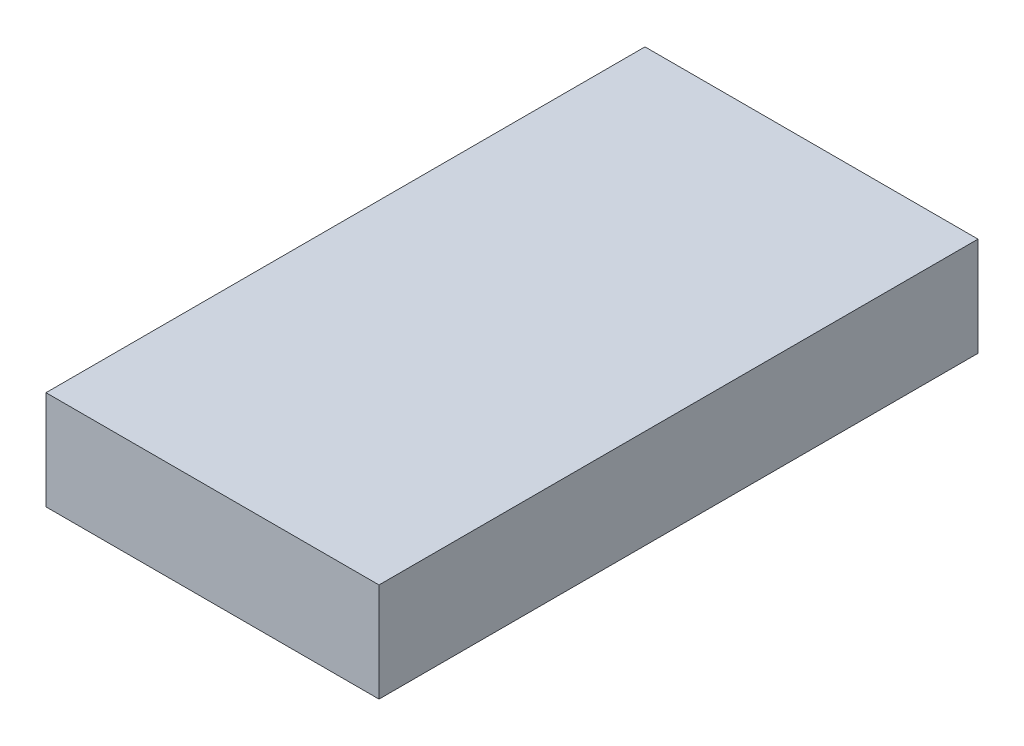
SolidWorks part; units mm, degrees
ref_plane "Front Plane" through (0, 0, 0) normal (0, 0, 1) x (1, 0, 0)
ref_plane "Top Plane" through (0, 0, 0) normal (0, 1, 0) x (1, 0, 0)
ref_plane "Right Plane" through (0, 0, 0) normal (1, 0, 0) x (0, 0, -1)
sketch "Sketch1" plane through (0, 0, 0) normal (0, 1, 0) x (1, 0, 0)
  line L1 (0, 0) -> (26, 0)
  line L2 (0, 0) -> (0, 46)
  line L3 (0, 46) -> (26, 46)
  line L4 (26, 0) -> (26, 46)
  dimension "D1" = 26
  dimension "D2" = 46
extrude "Boss-Extrude1" add sketch "Sketch1" along normal blind 5.8
sketch "Sketch2" plane through (0, 5.8, 0) normal (0, 1, 0) x (1, 0, 0)
  line L0 (0, 46) -> (0, 0) construction
  line L1 (0.65, 44.5) -> (25.35, 44.5)
  line L2 (0.65, 44.5) -> (0.65, -0.5)
  line L3 (0.65, -0.5) -> (25.35, -0.5)
  line L4 (25.35, 44.5) -> (25.35, -0.5)
  line L5 (26, 46) -> (0, 46) construction
  dimension "D1" = 24.7
  dimension "D2" = 45
  dimension "D3" = 0.65
  dimension "D4" = 1.5
extrude "Cut-Extrude1" cut sketch "Sketch2" against normal blind 5 from offset 0.4 offset against normal yes
sketch "Sketch3" plane through (0, 5.8, 0) normal (0, 1, 0) x (1, 0, 0)
  line L1 (28.0089, 48.3932) -> (-2.2911, 48.3932)
  line L2 (28.0089, 48.3932) -> (28.0089, -6.1068)
  line L3 (28.0089, -6.1068) -> (-2.2911, -6.1068)
  line L4 (-2.2911, 48.3932) -> (-2.2911, -6.1068)
  dimension "D1" = 30.3
  dimension "D2" = 54.5
extrude "Boss-Extrude2" add sketch "Sketch3" along normal blind 1
sketch "Sketch4" plane through (0, 5.8, 0) normal (0, -1, 0) x (1, 0, 0)
  line L0 (28.0089, -48.3932) -> (-2.2911, -48.3932) construction
  line L1 (-2.2911, 6.1068) -> (-1.2911, 6.1068)
  line L2 (-2.2911, 6.1068) -> (-2.2911, -48.3932)
  line L3 (-2.2911, -48.3932) -> (-1.2911, -48.3932)
  line L4 (-1.2911, 6.1068) -> (-1.2911, -48.3932)
  line L5 (27.0112, 6.1146) -> (28.0112, 6.1146)
  line L6 (27.0112, 6.1146) -> (27.0112, -46.8854)
  line L7 (27.0112, -46.8854) -> (28.0112, -46.8854)
  line L8 (28.0112, 6.1146) -> (28.0112, -46.8854)
  dimension "D1" = 1
extrude "Boss-Extrude3" add sketch "Sketch4" along normal blind 8 contours L2 L3 L4 L1
sketch "Sketch5" plane through (0, 5.8, 0) normal (0, -1, 0) x (1, 0, 0)
  line L0 (-1.2911, 6.1068) -> (-1.2911, -48.3932) construction
  line L1 (-1.2911, 6.1068) -> (28.0089, 6.1068)
  line L2 (-1.2911, 6.1068) -> (-1.2911, 5.1068)
  line L3 (-1.2911, 5.1068) -> (28.0089, 5.1068)
  line L4 (28.0089, 6.1068) -> (28.0089, 5.1068)
  line L5 (-1.2911, 6.1068) -> (28.0089, 6.1068) construction
  line L6 (28.0089, 6.1068) -> (28.0089, -48.3932) construction
  dimension "D1" = 1
extrude "Boss-Extrude4" add sketch "Sketch5" along normal blind 8
sketch "Sketch6" plane through (0, 5.8, 0) normal (0, -1, 0) x (1, 0, 0)
  line L0 (28.0089, -48.3932) -> (-1.2911, -48.3932) construction
  line L1 (28.0089, 5.1068) -> (27.0089, 5.1068)
  line L2 (28.0089, 5.1068) -> (28.0089, -48.3932)
  line L3 (28.0089, -48.3932) -> (27.0089, -48.3932)
  line L4 (27.0089, 5.1068) -> (27.0089, -48.3932)
  dimension "D1" = 1
extrude "Boss-Extrude5" add sketch "Sketch6" along normal blind 8
sketch "Sketch7" plane through (0, 5.8, 0) normal (0, -1, 0) x (1, 0, 0)
  line L0 (27.0089, 5.1068) -> (27.0089, -48.3932) construction
  line L1 (27.0089, -47.3932) -> (-1.2911, -47.3932)
  line L2 (27.0089, -47.3932) -> (27.0089, -48.3932)
  line L3 (27.0089, -48.3932) -> (-1.2911, -48.3932)
  line L4 (-1.2911, -47.3932) -> (-1.2911, -48.3932)
  dimension "D1" = 1
extrude "Boss-Extrude6" add sketch "Sketch7" along normal blind 8
sketch "Sketch8" plane through (0, 0, 0) normal (0, -1, 0) x (1, 0, 0)
  line L0 (0, 0) -> (26, 0) construction
  line L1 (2.7554, 0) -> (22.5963, 0)
  line L2 (2.7554, 0) -> (2.7554, -47.3932)
  line L3 (2.7554, -47.3932) -> (22.5963, -47.3932)
  line L4 (22.5963, 0) -> (22.5963, -47.3932)
  line L5 (26, -47.3932) -> (0, -47.3932) construction
extrude "Cut-Extrude2" cut sketch "Sketch8" against normal blind 2
sketch "Sketch9" plane through (0, 0, 0) normal (0, -1, 0) x (1, 0, 0)
  line L3 (25.385, 0.0281) -> (0.685, 0.0281)
  line L4 (25.385, 0.0281) -> (25.385, -25.189)
  line L5 (25.385, -25.189) -> (0.685, -25.189)
  line L6 (0.685, 0.0281) -> (0.685, -25.189)
  dimension "D1" = 24.7
extrude "Cut-Extrude3" cut sketch "Sketch9" against normal blind 1
